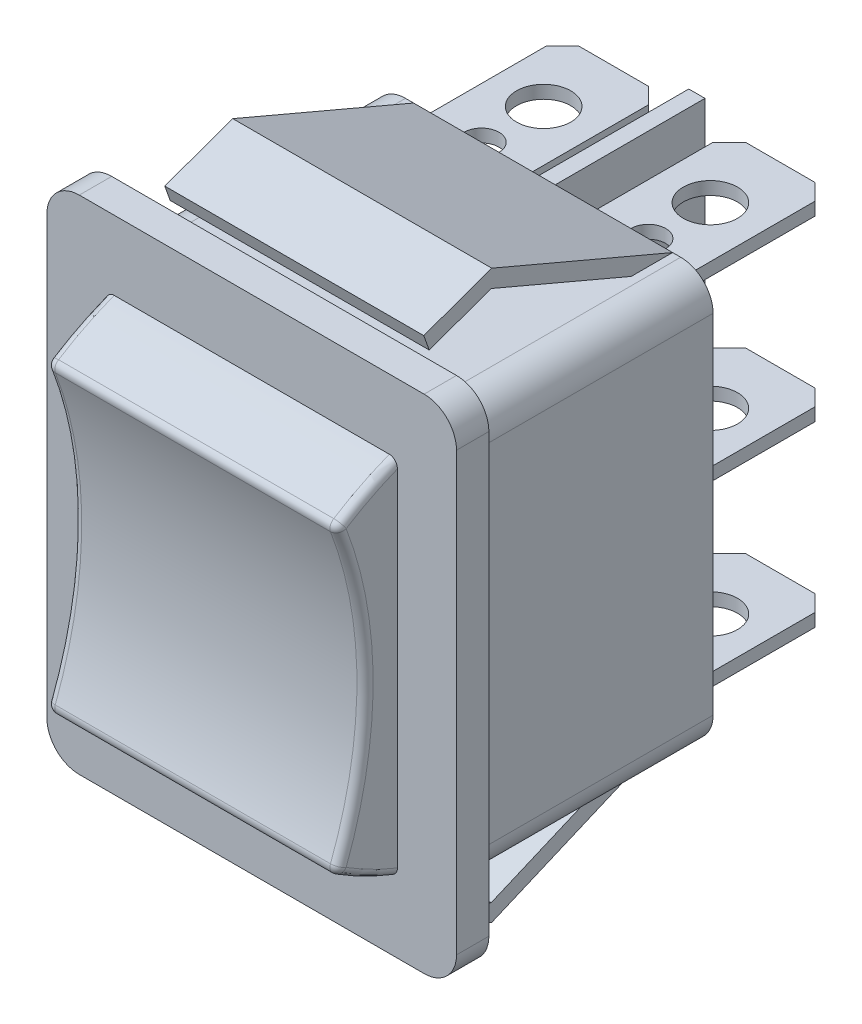
SolidWorks part; units mm, degrees
ref_plane "Front Plane" through (0, 0, 0) normal (0, 0, 1) x (1, 0, 0)
ref_plane "Top Plane" through (0, 0, 0) normal (0, 1, 0) x (1, 0, 0)
ref_plane "Right Plane" through (0, 0, 0) normal (1, 0, 0) x (0, 0, -1)
sketch "Sketch2" plane through (0, 0, 0) normal (0, 0, 1) x (1, 0, 0)
  line L1 (-12.65, 15.5) -> (12.65, 15.5)
  line L2 (-12.65, 15.5) -> (-12.65, -15.5)
  line L3 (-12.65, -15.5) -> (12.65, -15.5)
  line L4 (12.65, 15.5) -> (12.65, -15.5)
  line L5 (-12.65, 15.5) -> (12.65, -15.5) construction
  line L6 (-12.65, -15.5) -> (12.65, 15.5) construction
  point P0 (0, 0)
  dimension "D1" = 31
  dimension "D2" = 25.3
extrude "Boss-Extrude1" add sketch "Sketch2" along normal blind 2
sketch "Sketch3" plane through (0, 0, 0) normal (0, 0, 1) x (1, 0, 0)
  line L1 (-10.5, 12.75) -> (10.5, 12.75)
  line L2 (-10.5, 12.75) -> (-10.5, -12.75)
  line L3 (-10.5, -12.75) -> (10.5, -12.75)
  line L4 (10.5, 12.75) -> (10.5, -12.75)
  line L5 (-10.5, 12.75) -> (10.5, -12.75) construction
  line L6 (-10.5, -12.75) -> (10.5, 12.75) construction
  point P0 (0, 0)
  dimension "D1" = 25.5
  dimension "D2" = 21
extrude "Boss-Extrude2" add sketch "Sketch3" against normal blind 16
sketch "Sketch4" plane through (0, 0, 0) normal (1, 0, 0) x (0, 0, -1)
  line L0 (-2, -15.5) -> (-2, 15.5) construction
  line L1 (4.5714, 12.5) -> (25.5, 12.5)
  line L2 (4.5714, 12.5) -> (4.5714, -12.5)
  line L3 (4.5714, -12.5) -> (25.5, -12.5)
  line L4 (25.5, 12.5) -> (25.5, -12.5)
  line L5 (4.5714, 12.5) -> (25.5, -12.5) construction
  line L6 (4.5714, -12.5) -> (25.5, 12.5) construction
  point P0 (15.0357, 0)
  dimension "D1" = 25
  dimension "D2" = 27.5
extrude "Boss-Extrude3" add sketch "Sketch4" along normal mid plane 1
sketch "Sketch5" plane through (0, 0, 0) normal (0, 1, 0) x (1, 0, 0)
  line L0 (-12.65, -2) -> (12.65, -2) construction
  line L1 (8.3, 25.5) -> (2, 25.5)
  line L2 (8.3, 25.5) -> (8.3, 13.2281)
  line L3 (8.3, 13.2281) -> (2, 13.2281)
  line L4 (2, 25.5) -> (2, 13.2281)
  line L5 (8.3, 25.5) -> (2, 13.2281) construction
  line L6 (8.3, 13.2281) -> (2, 25.5) construction
  circle A0 centre (5.15, 17.35) radius 1.0759
  circle A1 centre (5.15, 21.1845) radius 1.6754
  point P0 (5.15, 19.3641)
  dimension "D1" = 27.5
  dimension "D2" = 6.3
  dimension "D3" = 5.15
extrude "Boss-Extrude4" add sketch "Sketch5" along normal mid plane 0.8 separate body
chamfer "Chamfer1" distance 1 angle 45 2 edges at (2, 0, -25.5) (8.3, 0, -25.5)
pattern_linear "LPattern1" count 2 spacing 11 along (0, -1, 0) count 2 spacing 11 along (0, 1, 0) of "Boss-Extrude4"
mirror "Mirror1" about plane through (0, 0, 0) normal (1, 0, 0) of bodies 106 105 104
sketch "Sketch7" plane through (0, 0, 0) normal (1, 0, 0) x (0, 0, -1)
  line L0 (16, -12.75) -> (4.8278, -17.5)
  line L1 (4.8278, -17.5) -> (0.6275, -15.9938)
  dimension "D1" = 17.5
extrude "Extrude-Thin1" add sketch "Sketch7" along normal mid plane 16 thin
mirror "Mirror2" about plane through (0, 0, 0) normal (0, 1, 0) of "Extrude-Thin1"
fillet "Fillet1" radius 2 8 edges at (12.65, 15.5, 1) (-12.65, 15.5, 1) (-12.65, -15.5, 1) (12.65, -15.5, 1) (-10.5, 12.75, -8) (-10.5, -12.75, -8) (10.5, 12.75, -8) (10.5, -12.75, -8)
sketch "Sketch8" plane through (0, 0, 0) normal (1, 0, 0) x (0, 0, -1)
  line L0 (-4.0009, 0) -> (-2, 0) construction
  line L1 (-2, -13.5) -> (-2, 13.5) construction
  line L2 (-2, -11.2101) -> (-2, 11.2101)
  line L3 (-4.0009, 0) -> (-4.0009, -3.2013) construction
  arc A0 (-5.7814, -9.26) -> (-5.7814, 9.26) centre (-28.9719, 0) ccw
  arc A1 (-5.7814, 9.26) -> (-2, 11.2101) centre (5.0294, -7.0622) cw
  arc A2 (-5.7814, -9.26) -> (-2, -11.2101) centre (5.0294, 7.0622) ccw
extrude "Boss-Extrude5" add sketch "Sketch8" along normal mid plane 18 separate body
fillet "Fillet2" radius 0.5 8 edges at (-9, 10.3381, 3.9438) (-9, 0, 4.0009) (-9, -10.3381, 3.9438) (9, 10.3381, 3.9438) (9, -10.3381, 3.9438) (9, 0, 4.0009) (0, 9.26, 5.7814) (0, -9.26, 5.7814)
